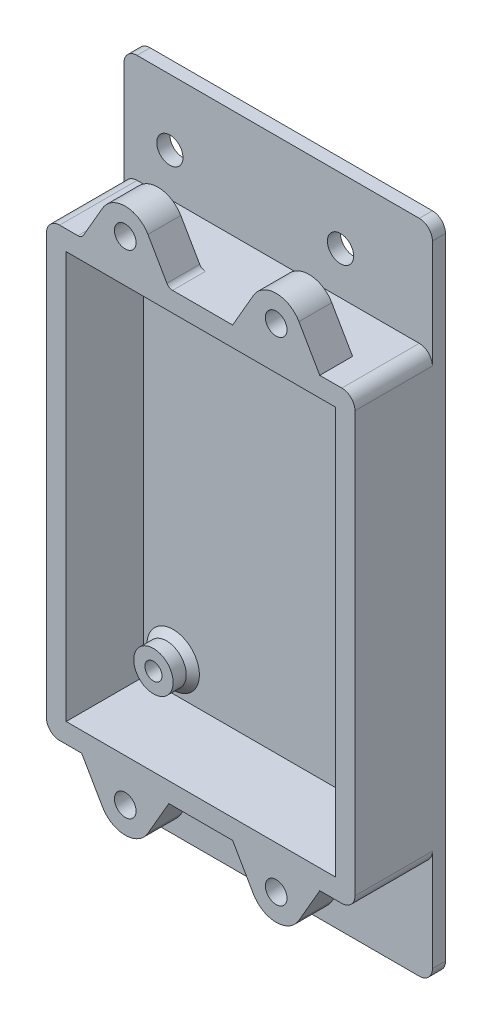
SolidWorks part; units mm, degrees
ref_plane "前视基准面" through (0, 0, 0) normal (0, 0, 1) x (1, 0, 0)
ref_plane "上视基准面" through (0, 0, 0) normal (0, 1, 0) x (1, 0, 0)
ref_plane "右视基准面" through (0, 0, 0) normal (1, 0, 0) x (0, 0, -1)
sketch "草图1" plane through (0, 0, 0) normal (0, 0, 1) x (1, 0, 0)
  line L1 (-20, -50) -> (20, -50)
  line L2 (-20, -50) -> (-20, 50)
  line L3 (-20, 50) -> (20, 50)
  line L4 (20, -50) -> (20, 50)
  line L5 (-20, -50) -> (20, 50) construction
  line L6 (-20, 50) -> (20, -50) construction
  line L7 (-13, -40) -> (13, -40) construction
  line L8 (-13, -40) -> (-13, 40) construction
  line L9 (-13, 40) -> (13, 40) construction
  line L10 (13, -40) -> (13, 40) construction
  line L11 (-13, -40) -> (13, 40) construction
  line L12 (-13, 40) -> (13, -40) construction
  circle A0 centre (-13, 40) radius 2
  circle A1 centre (13, 40) radius 2
  circle A2 centre (-13, -40) radius 2
  circle A3 centre (13, -40) radius 2
  point P0 (0, 0)
  point P6 (0, 0)
  dimension "D1" = 4
  dimension "D2" = 100
  dimension "D3" = 40
  dimension "D4" = 26
  dimension "D5" = 80
extrude "凸台-拉伸1" add sketch "草图1" along normal blind 2
sketch "草图2" plane through (0, 0, 2) normal (0, 0, 1) x (1, 0, 0)
  line L5 (-17, 30.5031) -> (-17, -31.4969)
  line L6 (-17, -31.4969) -> (24, -31.4969)
  line L7 (24, 30.5031) -> (24, -31.4969)
  line L8 (-17, 30.5031) -> (24, 30.5031)
  line L9 (24, 30.5031) -> (-17, -31.4969) construction
  line L10 (-12.5, -26.9969) -> (19.5, -26.9969) construction
  line L11 (-12.5, -26.9969) -> (-12.5, 26.0031) construction
  line L12 (-12.5, 26.0031) -> (19.5, 26.0031) construction
  line L13 (19.5, -26.9969) -> (19.5, 26.0031) construction
  line L14 (-12.5, 26.0031) -> (19.5, -26.9969) construction
  line L15 (-20, 33.5031) -> (-20, -34.4969)
  line L16 (-20, -34.4969) -> (27, -34.4969)
  line L17 (27, 33.5031) -> (27, -34.4969)
  line L18 (-20, 33.5031) -> (27, 33.5031)
  line L19 (-20, 50) -> (-20, -50) construction
  circle A0 centre (-12.5, 26.0031) radius 1.3 construction
  circle A1 centre (19.5, 26.0031) radius 1.3 construction
  circle A2 centre (19.5, -26.9969) radius 1.3 construction
  circle A3 centre (-12.5, -26.9969) radius 1.3 construction
  point P0 (3.5, -0.4969)
  point P1 (3.5, -0.4969)
  dimension "D5" = 2.6
  dimension "D1" = 41
  dimension "D2" = 62
  dimension "D3" = 32
  dimension "D4" = 53
  dimension "D6" = 3
extrude "凸台-拉伸2" add sketch "草图2" along normal blind 11.8
sketch "草图3" plane through (0, 0, 0) normal (0, 0, -1) x (-1, 0, 0)
  line L0 (-27, -34.4969) -> (-27, 33.5031) construction
  line L1 (-20, 50) -> (-27, 50)
  line L2 (-20, 50) -> (-20, -50)
  line L3 (-20, -50) -> (-27, -50)
  line L4 (-27, 50) -> (-27, -50)
  line L5 (20, -50) -> (-20, -50) construction
extrude "凸台-拉伸3" add sketch "草图3" against normal up to surface (2 mm away) up to face at (22.75, -0.4969, 2)
sketch "草图4" plane through (0, 0, 2) normal (0, 0, 1) x (1, 0, 0)
  circle A0 centre (-12.5, 26.0031) radius 3
  circle A1 centre (19.5, 26.0031) radius 3
  circle A2 centre (19.5, -26.9969) radius 3
  circle A3 centre (-12.5, -26.9969) radius 3
  circle A4 centre (-12.5, -26.9969) radius 1.3 construction
  circle A5 centre (19.5, -26.9969) radius 1.3 construction
  circle A6 centre (19.5, 26.0031) radius 1.3 construction
  circle A7 centre (-12.5, 26.0031) radius 1.3 construction
  circle A8 centre (-12.5, -26.9969) radius 1.3
  circle A9 centre (19.5, -26.9969) radius 1.3
  circle A10 centre (19.5, 26.0031) radius 1.3
  circle A11 centre (-12.5, 26.0031) radius 1.3
  dimension "D1" = 6
extrude "凸台-拉伸4" add sketch "草图4" along normal blind 3
sketch "草图5" plane through (0, 0, 5) normal (0, 0, 1) x (1, 0, 0)
  circle A0 centre (-12.5, -26.9969) radius 1.3 construction
  circle A1 centre (19.5, -26.9969) radius 1.3 construction
  circle A2 centre (19.5, 26.0031) radius 1.3 construction
  circle A3 centre (-12.5, 26.0031) radius 1.3 construction
  circle A4 centre (-12.5, -26.9969) radius 1.3
  circle A5 centre (19.5, -26.9969) radius 1.3
  circle A6 centre (19.5, 26.0031) radius 1.3
  circle A7 centre (-12.5, 26.0031) radius 1.3
extrude "切除-拉伸1" cut sketch "草图5" against normal blind 3.5
sketch "草图6" plane through (0, 0, 13.8) normal (0, 0, 1) x (1, 0, 0)
  line L0 (-14.6395, 33.5031) -> (-1.3605, 33.5031)
  line L4 (-14.6395, 33.5031) -> (-11.4641, 39.0031)
  line L5 (-4.5359, 39.0031) -> (-1.3605, 33.5031)
  line L6 (27, 33.5031) -> (-20, 33.5031) construction
  line L7 (27, 33.5031) -> (-20, 33.5031) construction
  line L8 (-20, 33.5031) -> (-20, -34.4969) construction
  circle A0 centre (-8, 37.0031) radius 1.65
  arc A1 (-11.4641, 39.0031) -> (-4.5359, 39.0031) centre (-8, 37.0031) cw
  dimension "D1" = 3.3
  dimension "D5" = 4
  dimension "D2" = 3.5
  dimension "D3" = 12
  dimension "D4" = 60
extrude "凸台-拉伸5" add sketch "草图6" against normal blind 5
sketch "草图7" plane through (0, 0, 8.8) normal (0, 0, -1) x (-1, 0, 0)
  line L1 (6.3257, 39.9031) -> (4.6514, 37.0031)
  line L2 (4.6514, 37.0031) -> (6.3257, 34.1031)
  line L3 (6.3257, 34.1031) -> (9.6743, 34.1031)
  line L4 (9.6743, 34.1031) -> (11.3486, 37.0031)
  line L5 (11.3486, 37.0031) -> (9.6743, 39.9031)
  line L6 (9.6743, 39.9031) -> (6.3257, 39.9031)
  circle A0 centre (8, 37.0031) radius 2.9 construction
  dimension "D1" = 5.8
extrude "切除-拉伸2" cut sketch "草图7" against normal blind 2
fillet "圆角1" radius 1 2 edges at (-1.3605, 33.5031, 11.3) (-14.6395, 33.5031, 11.3)
ref_plane "基准面1" through (3.5, 0, 0) normal (1, 0, 0) x (0, 0, -1)
ref_plane "基准面2" through (0, -0.4969, 0) normal (0, -1, 0) x (-1, 0, 0)
mirror "镜向1" about plane through (3.5, 0, 0) normal (1, 0, 0) of "凸台-拉伸5", "切除-拉伸2"
mirror "镜向5" about plane through (0, -0.4969, 0) normal (0, -1, 0) of "镜向1", "切除-拉伸2", "凸台-拉伸5"
fillet "圆角2" radius 2 8 edges at (27, -50, 1) (-20, -50, 1) (-20, -34.4969, 7.9) (27, -34.4969, 7.9) (27, 33.5031, 7.9) (-20, 33.5031, 7.9) (27, 50, 1) (-20, 50, 1)
chamfer "倒角1" distance 1 angle 45 4 edges at (16.5, -26.9969, 2) (-15.5, -26.9969, 2) (-15.5, 26.0031, 2) (16.5, 26.0031, 2)
